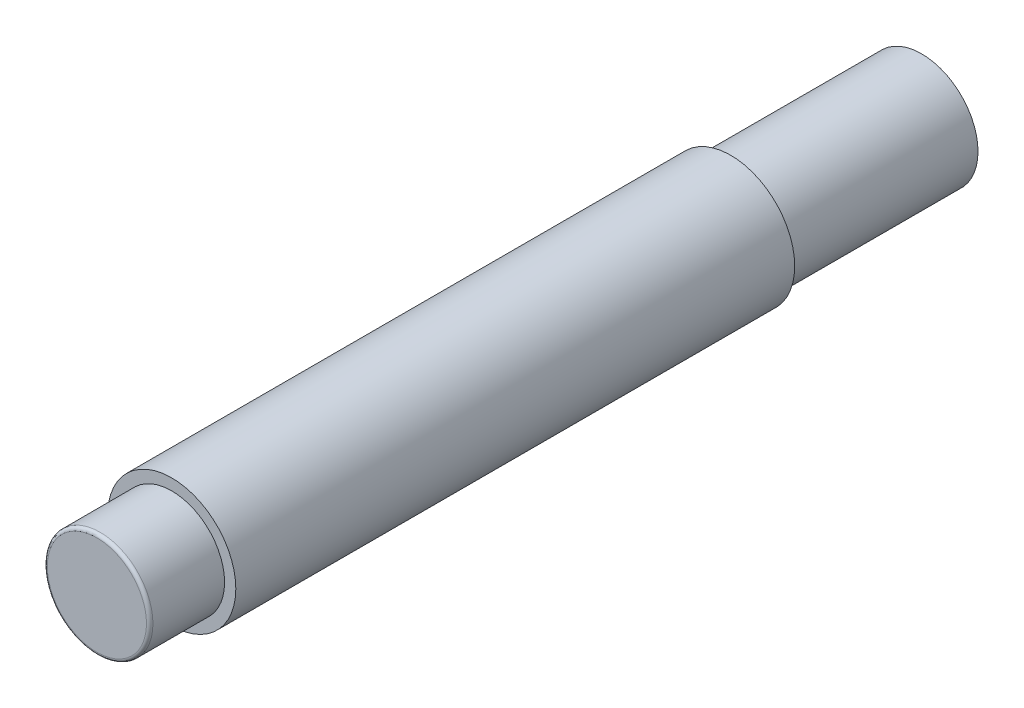
SolidWorks part; units mm, degrees
ref_plane "Front Plane" through (0, 0, 0) normal (0, 0, 1) x (1, 0, 0)
ref_plane "Top Plane" through (0, 0, 0) normal (0, 1, 0) x (1, 0, 0)
ref_plane "Right Plane" through (0, 0, 0) normal (1, 0, 0) x (0, 0, -1)
sketch "Sketch1" plane through (0, 0, 0) normal (1, 0, 0) x (0, 0, -1)
  line L0 (-22.5915, 0) -> (10.3013, 0) construction
  line L1 (0, 0) -> (0, 3.265)
  line L2 (0, 3.265) -> (4.63, 3.265)
  line L3 (4.63, 3.265) -> (4.63, 3.96)
  line L4 (4.63, 3.96) -> (39.19, 3.96)
  line L5 (39.19, 3.96) -> (39.19, 3.485)
  line L6 (39.19, 3.485) -> (51, 3.485)
  line L7 (51, 3.485) -> (51, 0)
  line L8 (51, 0) -> (0, 0)
  dimension "D1" = 3.265
  dimension "D2" = 3.96
  dimension "D3" = 3.485
  dimension "D4" = 51
  dimension "D5" = 4.63
  dimension "D6" = 11.81
revolve "Revolve1" add sketch "Sketch1" angle 360 about L0
fillet "Fillet1" radius 0.2 1 edges at (3.265, 0, 0)
